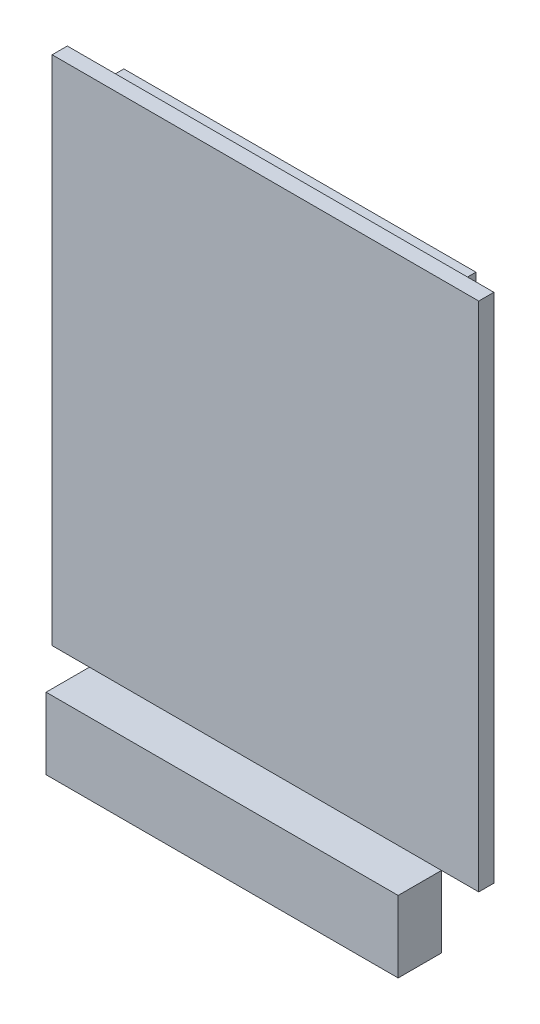
SolidWorks part; units mm, degrees
ref_plane "Front Plane" through (0, 0, 0) normal (0, 0, 1) x (1, 0, 0)
ref_plane "Top Plane" through (0, 0, 0) normal (0, 1, 0) x (1, 0, 0)
ref_plane "Right Plane" through (0, 0, 0) normal (1, 0, 0) x (0, 0, -1)
sketch "Sketch1" plane through (0, 0, 0) normal (0, 0, 1) x (1, 0, 0)
  line L1 (0, 59.9948) -> (50.0126, 59.9948)
  line L2 (0, 59.9948) -> (0, 0)
  line L3 (0, 0) -> (50.0126, 0)
  line L4 (50.0126, 59.9948) -> (50.0126, 0)
  dimension "D1" = 50.0126
  dimension "D2" = 59.9948
extrude "Boss-Extrude1" add sketch "Sketch1" along normal blind 1.778
sketch "Sketch2" plane through (0, 0, 1.778) normal (0, 0, 1) x (1, 0, 0)
  line L6 (0, 0) -> (50.0126, 0) construction
  line L7 (4.3688, 0) -> (45.6438, 0)
  line L9 (4.3688, 0) -> (4.3688, -8.382)
  line L10 (4.3688, -8.382) -> (45.6438, -8.382)
  line L11 (45.6438, 0) -> (45.6438, -8.382)
  point P12 (25.0063, 0)
  dimension "D4" = 8.382
  dimension "D5" = 41.275
extrude "Boss-Extrude2" add sketch "Sketch2" along normal blind 5.08 separate body
sketch "Sketch3" plane through (0, 0, 0) normal (0, 0, -1) x (-1, 0, 0)
  line L0 (-25.0063, 59.9948) -> (-25.0063, 58.7248) construction
  line L1 (-45.6438, 58.7248) -> (-4.3688, 58.7248)
  line L2 (-45.6438, 58.7248) -> (-45.6438, 53.6448)
  line L3 (-45.6438, 53.6448) -> (-4.3688, 53.6448)
  line L4 (-4.3688, 58.7248) -> (-4.3688, 53.6448)
  line L8 (-50.0126, 59.9948) -> (0, 59.9948) construction
  dimension "D1" = 5.08
  dimension "D2" = 41.275
  dimension "D3" = 1.27
extrude "Boss-Extrude3" add sketch "Sketch3" along normal blind 2.2606
